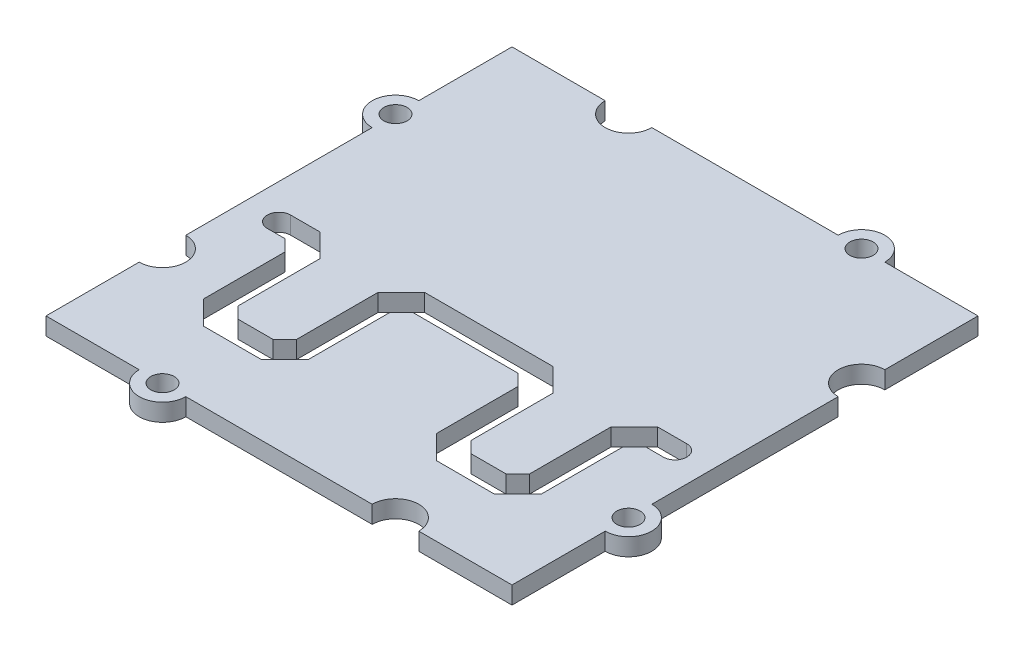
SolidWorks part; units mm, degrees
ref_plane "Plan de face" through (0, 0, 0) normal (0, 0, 1) x (1, 0, 0)
ref_plane "Plan de dessus" through (0, 0, 0) normal (0, 1, 0) x (1, 0, 0)
ref_plane "Plan de droite" through (0, 0, 0) normal (1, 0, 0) x (0, 0, -1)
sketch "Esquisse1" plane through (0, 0, 0) normal (0, 1, 0) x (1, 0, 0)
  line L0 (-32.2051, 0) -> (35.4872, 0) construction
  line L1 (0, 32.1026) -> (0, -26.359) construction
  line L2 (-10, 32.1026) -> (-10, -26.359) construction
  line L3 (-20, 20) -> (-12, 20)
  line L4 (-20, 20) -> (-20, 12)
  line L5 (-20, -20) -> (-12, -20)
  line L6 (20, 12.0014) -> (20, 20)
  line L7 (10, 32.1026) -> (10, -26.359) construction
  line L8 (-25.641, 10) -> (23.5897, 10) construction
  line L9 (-25.641, -10) -> (23.5897, -10) construction
  line L10 (20, -8) -> (20, 7.9986)
  line L13 (12, 20) -> (20, 20)
  line L14 (20, -12) -> (20, -20)
  line L17 (-8, -20) -> (8, -20)
  line L18 (-20, 8) -> (-20, -8)
  line L19 (-20, -12) -> (-20, -20)
  line L21 (12, -20) -> (20, -20)
  line L24 (-8, 20) -> (8, 20)
  line L25 (-17, -4) -> (-15.5, -4)
  line L26 (-17, -2) -> (-14.5, -2)
  line L27 (-11.5, -12) -> (-8.5, -12)
  line L28 (-12.5, -14) -> (-7.5, -14)
  line L29 (-5.5, -5) -> (-5.5, -12)
  line L30 (-7.5, -4) -> (-7.5, -11)
  line L31 (-12.5, -4) -> (-12.5, -11)
  line L32 (-14.5, -5) -> (-14.5, -12)
  line L33 (-5.5, -2) -> (5.5, -2)
  line L34 (-4.5, -4) -> (4.5, -4)
  line L35 (5.5, -5) -> (4.5, -4)
  line L36 (-14.5, -2) -> (-12.5, -4)
  line L37 (-5.5, -2) -> (-7.5, -4)
  line L38 (-14.5, -12) -> (-12.5, -14)
  line L39 (5.5, -5) -> (5.5, -12)
  line L40 (-5.5, -12) -> (-7.5, -14)
  line L41 (-15.5, -4) -> (-14.5, -5)
  line L42 (-12.5, -11) -> (-11.5, -12)
  line L43 (-7.5, -11) -> (-8.5, -12)
  line L44 (-5.5, -5) -> (-4.5, -4)
  line L45 (5.5, -12) -> (7.5, -14)
  line L46 (12.5, -14) -> (7.5, -14)
  line L47 (14.5, -12) -> (12.5, -14)
  line L48 (14.5, -5) -> (14.5, -12)
  line L49 (15.5, -4) -> (14.5, -5)
  line L50 (17, -4) -> (15.5, -4)
  line L51 (17, -2) -> (14.5, -2)
  line L52 (14.5, -2) -> (12.5, -4)
  line L53 (12.5, -4) -> (12.5, -11)
  line L54 (12.5, -11) -> (11.5, -12)
  line L55 (11.5, -12) -> (8.5, -12)
  line L56 (7.5, -11) -> (8.5, -12)
  line L57 (7.5, -4) -> (7.5, -11)
  line L58 (5.5, -2) -> (7.5, -4)
  arc A0 (-12, 20) -> (-8, 20) centre (-10, 20) ccw
  arc A1 (-20, 12) -> (-20, 8) centre (-20, 10) ccw
  arc A2 (12, 20) -> (8, 20) centre (10, 20) ccw
  arc A3 (12, -20) -> (8, -20) centre (10, -20) ccw
  circle A4 centre (-10, -20) radius 1
  arc A5 (20, 12.0014) -> (20, 7.9986) centre (20, 10) ccw
  circle A6 centre (20, -10) radius 1
  arc A7 (-20, -12) -> (-20, -8) centre (-20, -10) ccw
  circle A9 centre (-20, 10) radius 1
  circle A10 centre (10, 20) radius 1
  arc A11 (20, -12) -> (20, -8) centre (20, -10) ccw
  arc A12 (-17, -2) -> (-17, -4) centre (-17, -3) ccw
  arc A13 (17, -2) -> (17, -4) centre (17, -3) cw
  arc A15 (-12, -20) -> (-8, -20) centre (-10, -20) ccw
  point P34 (-7.5, -2)
  point P38 (-5.5, -14)
  point P54 (0, -4)
  point P55 (-14.5, -14)
  point P57 (-12.5, -12)
  point P60 (-14.5, -4)
  point P61 (-12.5, -2)
  point P64 (-7.5, -12)
  point P65 (-5.5, -4)
  point P97 (0, -2)
  dimension "D7" = 2
  dimension "D8" = 2
  dimension "D13" = 40
  dimension "D15" = 2.0014
  dimension "D16" = 4
  dimension "D26" = 2
  dimension "D27" = 4
  dimension "D36" = 4
  dimension "D37" = 2
  dimension "D9" = 2
  dimension "D10" = 2
  dimension "D11" = 2
  dimension "D12" = 2
  dimension "D1" = 40
  dimension "D3" = 10
  dimension "D4" = 10
  dimension "D5" = 10
  dimension "D6" = 10
  dimension "D17" = 16
  dimension "D18" = 2
  dimension "D19" = 8
  dimension "D20" = 2
  dimension "D21" = 5.5
  dimension "D22" = 17
  dimension "D23" = 2
  dimension "D24" = 2
  dimension "D25" = 5
extrude "Boss.-Extru.1" add sketch "Esquisse1" along normal blind 1.5
